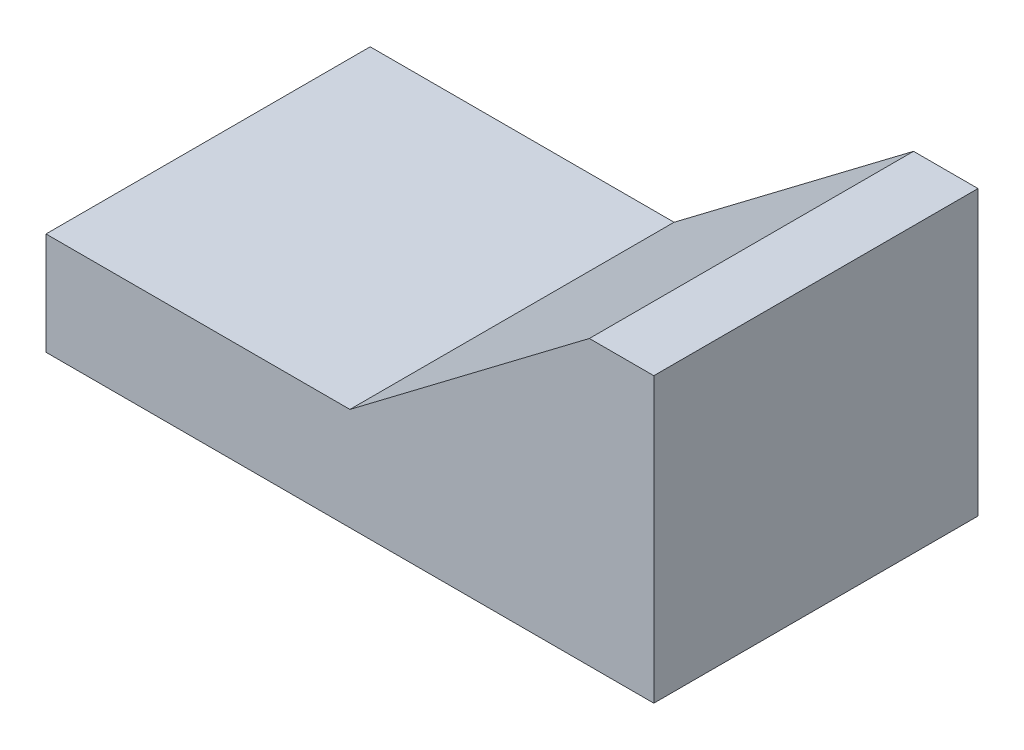
SolidWorks part; units mm, degrees
ref_plane "Ön Düzlem" through (0, 0, 0) normal (0, 0, 1) x (1, 0, 0)
ref_plane "Üst Düzlem" through (0, 0, 0) normal (0, 1, 0) x (1, 0, 0)
ref_plane "Sağ Düzlem" through (0, 0, 0) normal (1, 0, 0) x (0, 0, -1)
sketch "Çizim1" plane through (0, 0, 0) normal (0, 0, 1) x (1, 0, 0)
  line L1 (-7.0851, -1.5) -> (7.9149, -1.5)
  line L2 (-7.0851, -1.5) -> (-7.0851, 1.0294)
  line L3 (-7.0851, 1.0294) -> (0.4149, 1.0294)
  line L4 (7.9149, -1.5) -> (7.9149, 5.5)
  line L5 (7.9149, 5.5) -> (6.3242, 5.5)
  line L6 (6.3242, 5.5) -> (0.4149, 1.0294)
  dimension "D1" = 15
  dimension "D2" = 7
extrude "Yükseklik-Ekstrüzyon1" add sketch "Çizim1" along normal blind 8
